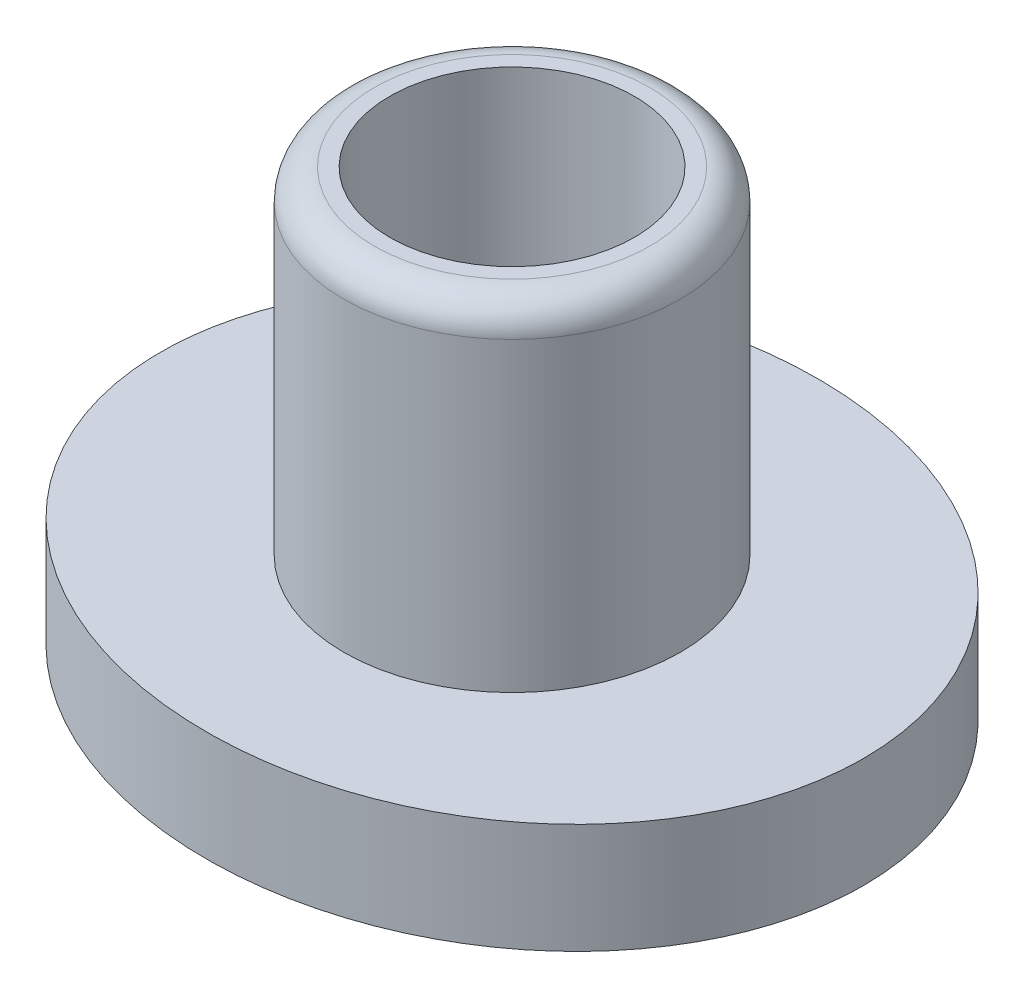
SolidWorks part; units mm, degrees
ref_plane "Front Plane" through (0, 0, 0) normal (0, 0, 1) x (1, 0, 0)
ref_plane "Top Plane" through (0, 0, 0) normal (0, 1, 0) x (1, 0, 0)
ref_plane "Right Plane" through (0, 0, 0) normal (1, 0, 0) x (0, 0, -1)
sketch "Sketch1" plane through (0, 0, 0) normal (0, 1, 0) x (1, 0, 0)
  ellipse E0 centre (0, 0) end of major axis (5.75, 0) minor radius 5
  dimension "D1" = 10
  dimension "D2" = 11.5
extrude "Boss-Extrude1" add sketch "Sketch1" along normal blind 1.8
sketch "Sketch2" plane through (0, 1.8, 0) normal (0, 1, 0) x (1, 0, 0)
  circle A0 centre (0, 0) radius 2.75
  dimension "D1" = 5.5
extrude "Boss-Extrude2" add sketch "Sketch2" along normal blind 5.5
sketch "Sketch3" plane through (0, 7.3, 0) normal (0, 1, 0) x (1, 0, 0)
  circle A0 centre (0, 0) radius 2
  dimension "D1" = 4
extrude "Cut-Extrude1" cut sketch "Sketch3" against normal through all
fillet "Fillet1" radius 0.25 1 edges at (0, 0, 2)
fillet "Fillet2" radius 0.5 1 edges at (0, 7.3, 2.75)
